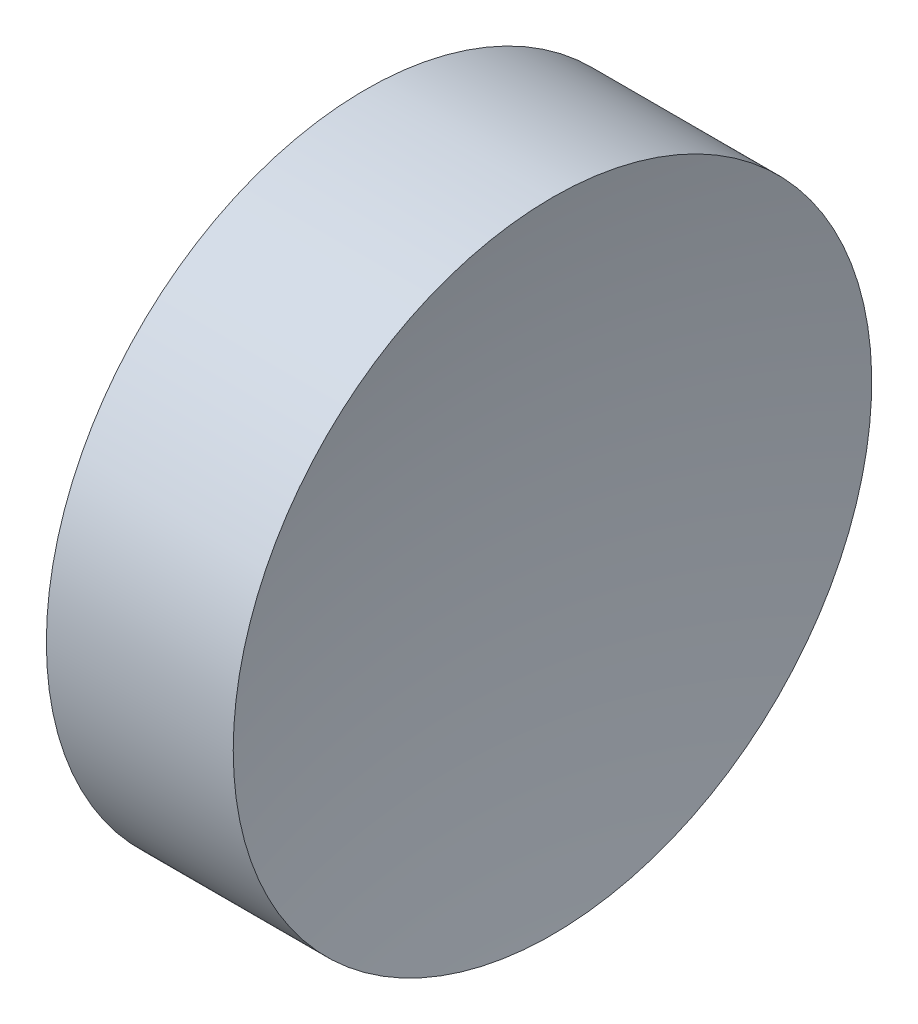
SolidWorks part; units mm, degrees
ref_plane "前视基准面" through (0, 0, 0) normal (0, 0, 1) x (1, 0, 0)
ref_plane "上视基准面" through (0, 0, 0) normal (0, 1, 0) x (1, 0, 0)
ref_plane "右视基准面" through (0, 0, 0) normal (1, 0, 0) x (0, 0, -1)
sketch "草图1" plane through (0, 0, 0) normal (0, 0, 1) x (1, 0, 0)
  line L0 (108.9851, 69.378) -> (132.7763, 69.378) construction
  line L1 (115.0927, 69.378) -> (115.0927, 81.878)
  line L2 (115.0927, 81.878) -> (122.4092, 81.878)
  line L3 (121.0927, 69.378) -> (115.0927, 69.378)
  arc A0 (122.4092, 81.878) -> (121.0927, 69.378) centre (181.0927, 69.378) ccw
  dimension "D1" = 7.3165
  dimension "D2" = 6
revolve "旋转1" add sketch "草图1" angle 360 about L0
